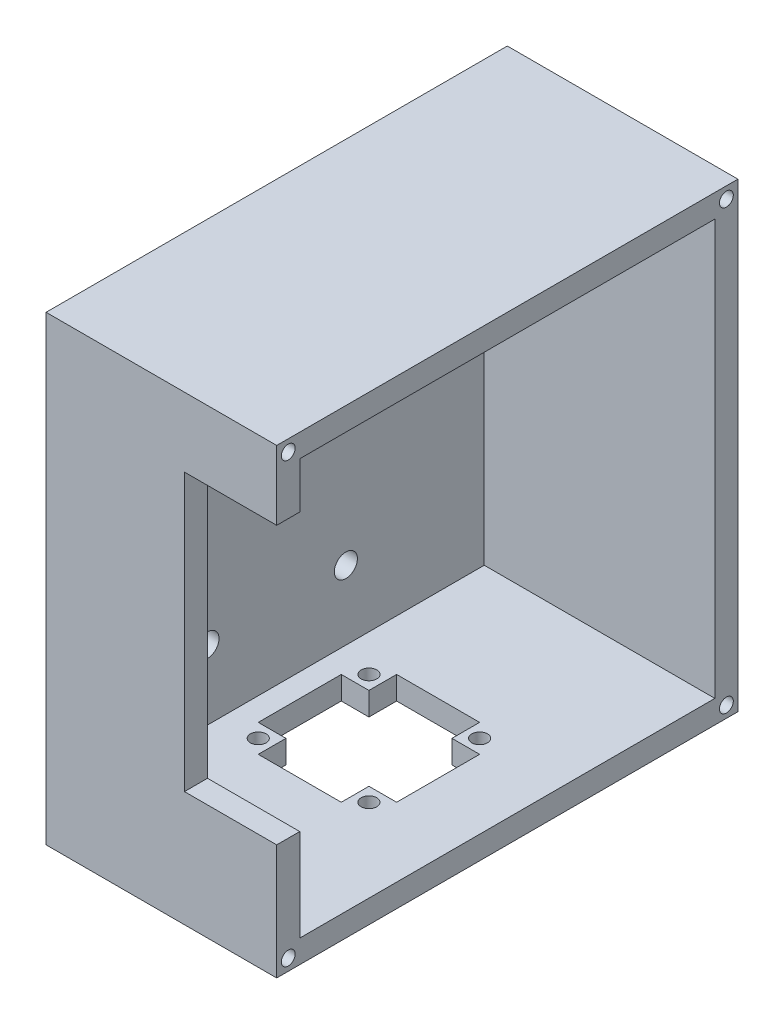
SolidWorks part; units mm, degrees
ref_plane "Front Plane" through (0, 0, 0) normal (0, 0, 1) x (1, 0, 0)
ref_plane "Top Plane" through (0, 0, 0) normal (0, 1, 0) x (1, 0, 0)
ref_plane "Right Plane" through (0, 0, 0) normal (1, 0, 0) x (0, 0, -1)
ref_plane "Plane1" through (0, 0, 0) normal (0, 0, 1) x (1, 0, 0)
sketch "Sketch7" plane through (0, 0, 0) normal (1, 0, 0) x (0, 0, -1)
  line L1 (-50, 50) -> (50, 50)
  line L2 (-50, 50) -> (-50, -50)
  line L3 (-50, -50) -> (50, -50)
  line L4 (50, 50) -> (50, -50)
  dimension "D1" = 100
  dimension "D2" = 100
  dimension "D3" = 50
  dimension "D4" = 50
extrude "Boss-Extrude2" add sketch "Sketch7" along normal blind 10
sketch "Sketch8" plane through (10, 0, 0) normal (1, 0, 0) x (0, 0, -1)
  line L0 (-45, 45) -> (-45, -45)
  line L1 (-50, 50) -> (50, 50)
  line L2 (-50, 50) -> (-50, -50)
  line L3 (-50, -50) -> (50, -50)
  line L4 (50, 50) -> (50, -50)
  line L5 (-45, -45) -> (45, -45)
  line L6 (45, 45) -> (45, -45)
  line L7 (-45, 45) -> (45, 45)
  dimension "D1" = 5
extrude "Boss-Extrude3" add sketch "Sketch8" along normal blind 50
chamfer "Chamfer1" distance 10 angle 45 4 edges at (0, -50, 0) (0, 0, -50) (0, 50, 0) (0, 0, 50)
sketch "Sketch14" plane through (0, 0, 0) normal (-1, 0, 0) x (0, 0, 1)
  line L0 (-25, 32.5) -> (25, 32.5) construction
  line L1 (-25, 37.5) -> (25, 37.5)
  line L2 (-25, 27.5) -> (25, 27.5)
  line L3 (0, -5.5) -> (0, 5.5) construction
  line L4 (40, 40) -> (-40, 40) construction
  arc A0 (-25, 37.5) -> (-25, 27.5) centre (-25, 32.5) ccw
  arc A1 (25, 27.5) -> (25, 37.5) centre (25, 32.5) ccw
  point P2 (0, 32.5)
  dimension "D2" = 5
  dimension "D1" = 50
  dimension "D3" = 25
  dimension "D4" = 2.5
extrude "Cut-Extrude5" cut sketch "Sketch14" against normal blind 15
fillet "Fillet3" radius 1 8 edges at (0, 32.5, -30) (0, 37.5, 0) (0, 32.5, 30) (0, 27.5, 0) (10, 32.5, 30) (10, 37.5, 0) (10, 32.5, -30) (10, 27.5, 0)
sketch "Sketch16" plane through (0, -50, 0) normal (0, -1, 0) x (1, 0, 0)
  line L0 (5.5, 0) -> (-5.5, 0) construction
  line L1 (15, 15) -> (45, 15)
  line L2 (15, 15) -> (15, -15)
  line L3 (15, -15) -> (45, -15)
  line L4 (45, 15) -> (45, -15)
  line L5 (0, -40) -> (0, 40) construction
  dimension "D1" = 30
  dimension "D2" = 30
  dimension "D3" = 15
  dimension "D4" = 15
extrude "Cut-Extrude6" cut sketch "Sketch16" against normal blind 10
sketch "Sketch17" plane through (0, -50, 0) normal (0, -1, 0) x (1, 0, 0)
  line L1 (15, 15) -> (21, 15)
  line L2 (15, 15) -> (15, 9)
  line L3 (15, 9) -> (21, 9)
  line L4 (21, 15) -> (21, 9)
  circle A0 centre (18, 12) radius 1.7
  point P7 (18, 9)
  dimension "D3" = 3.4
  dimension "D4" = 3
  dimension "D5" = 3
  dimension "D1" = 6
  dimension "D2" = 6
extrude "Boss-Extrude4" add sketch "Sketch17" against normal blind 5
pattern_linear "LPattern2" count 2 spacing 24 along (1, 0, 0) count 2 spacing 24 along (0, 0, -1) of "Boss-Extrude4"
sketch "Sketch18" plane through (0, 0, 0) normal (-1, 0, 0) x (0, 0, 1)
  line L0 (0, -5.5) -> (0, 5.5) construction
  line L1 (-50, 50) -> (50, 50) construction
  circle A0 centre (-15, 20) radius 2.5
  point P6 (0, 0)
  dimension "D1" = 5
  dimension "D2" = 15
  dimension "D3" = 30
extrude "Cut-Extrude7" cut sketch "Sketch18" against normal blind 10
pattern_linear "LPattern3" count 2 spacing 30 along (0, 0, 1) count 2 spacing 50 along (0, -1, 0) of "Cut-Extrude7"
sketch "Sketch19" plane through (0, 0, 50) normal (0, 0, 1) x (1, 0, 0)
  line L0 (60, 50) -> (60, -50) construction
  line L1 (60, 35) -> (40, 35)
  line L2 (60, 35) -> (60, -25)
  line L3 (60, -25) -> (40, -25)
  line L4 (40, 35) -> (40, -25)
  line L5 (60, 50) -> (10, 50) construction
  dimension "D1" = 20
  dimension "D2" = 15
  dimension "D3" = 60
extrude "Cut-Extrude8" cut sketch "Sketch19" against normal blind 10
sketch "Sketch20" plane through (60, 0, 0) normal (1, 0, 0) x (0, 0, -1)
  line L0 (-50, 50) -> (-50, 35) construction
  line L1 (50, 50) -> (-50, 50) construction
  circle A0 centre (-47.5, 47.5) radius 1.5
  dimension "D1" = 3
  dimension "D2" = 2.5
  dimension "D3" = 2.5
extrude "Cut-Extrude9" cut sketch "Sketch20" against normal blind 5
pattern_linear "LPattern4" count 2 spacing 95 along (0, 0, -1) count 2 spacing 95 along (0, -1, 0) of "Cut-Extrude9"
